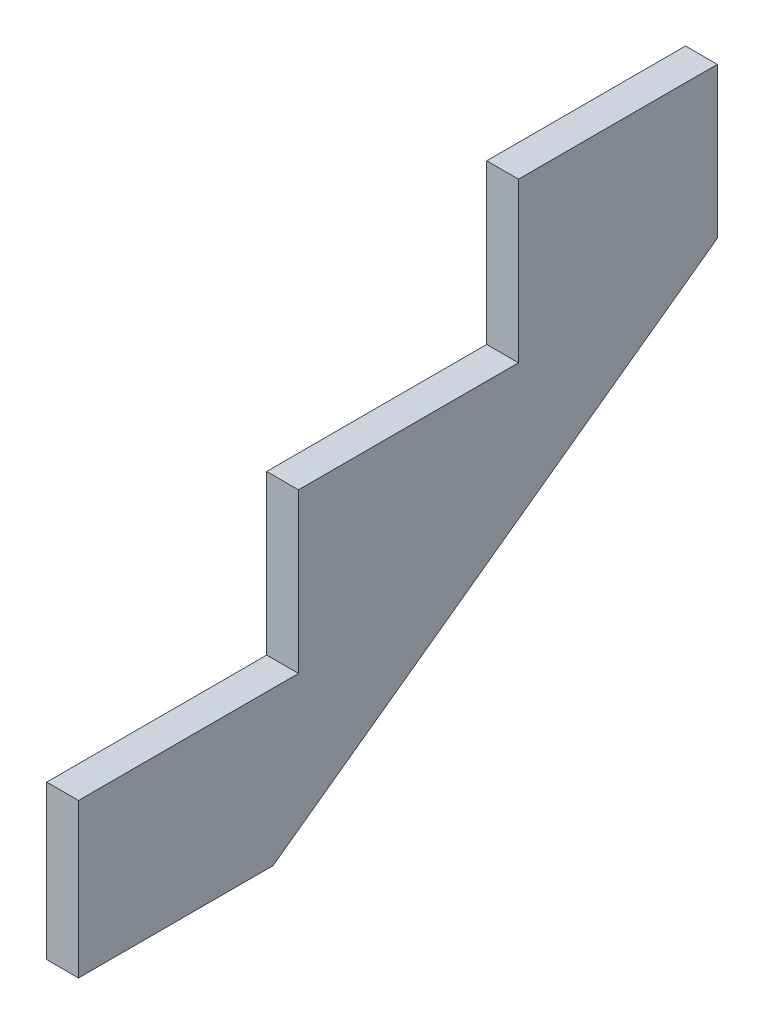
SolidWorks part; units mm, degrees
ref_plane "Front Plane" through (0, 0, 0) normal (0, 0, 1) x (1, 0, 0)
ref_plane "Top Plane" through (0, 0, 0) normal (0, 1, 0) x (1, 0, 0)
ref_plane "Right Plane" through (0, 0, 0) normal (1, 0, 0) x (0, 0, -1)
sketch "Sketch1" plane through (0, 0, 0) normal (1, 0, 0) x (0, 0, -1)
  line L0 (233.0145, 0) -> (765.175, 384.6943)
  line L1 (765.175, 565.15) -> (527.05, 565.15)
  line L6 (0, 0) -> (0, 184.15)
  line L7 (0, 184.15) -> (263.525, 184.15)
  line L10 (263.525, 184.15) -> (263.525, 374.65)
  line L11 (263.525, 374.65) -> (527.05, 374.65)
  line L14 (527.05, 374.65) -> (527.05, 565.15)
  line L15 (527.05, 565.15) -> (765.175, 565.15)
  line L17 (527.05, 374.65) -> (504.825, 374.65)
  line L18 (527.05, 374.65) -> (527.05, 565.15)
  line L21 (504.825, 374.65) -> (263.525, 374.65)
  line L25 (263.525, 184.15) -> (241.3, 184.15)
  line L26 (263.525, 184.15) -> (263.525, 374.65)
  line L29 (241.3, 184.15) -> (0, 184.15)
  line L34 (0, 0) -> (0, 184.15)
  line L37 (527.05, 565.15) -> (765.175, 565.15)
  line L38 (527.05, 565.15) -> (527.05, 374.65)
  line L40 (765.175, 565.15) -> (765.175, 384.6943)
  line L41 (0, 0) -> (233.0145, 0)
  line L42 (0, 0) -> (0, 184.15)
  line L43 (0, 184.15) -> (263.525, 184.15)
  dimension "D1" = 238.125
  dimension "D2" = 184.15
  dimension "D3" = 190.5
  dimension "D4" = 263.525
  dimension "D5" = 263.525
  dimension "D6" = 285.75
  dimension "D7" = 180.4557
  dimension "D8" = 565.15
  dimension "D9" = 765.175
  dimension "D10" = 285.75
  dimension "D11" = 131.3647
  dimension "D12" = 131.3647
  dimension "D13" = 233.0145
  dimension "D14" = 951.2556
  dimension "D17" = 190.5
extrude "Boss-Extrude2" add sketch "Sketch1" along normal blind 38.1 contours L6 L41 L0 L40 L1 L14 L11 L10 L7
